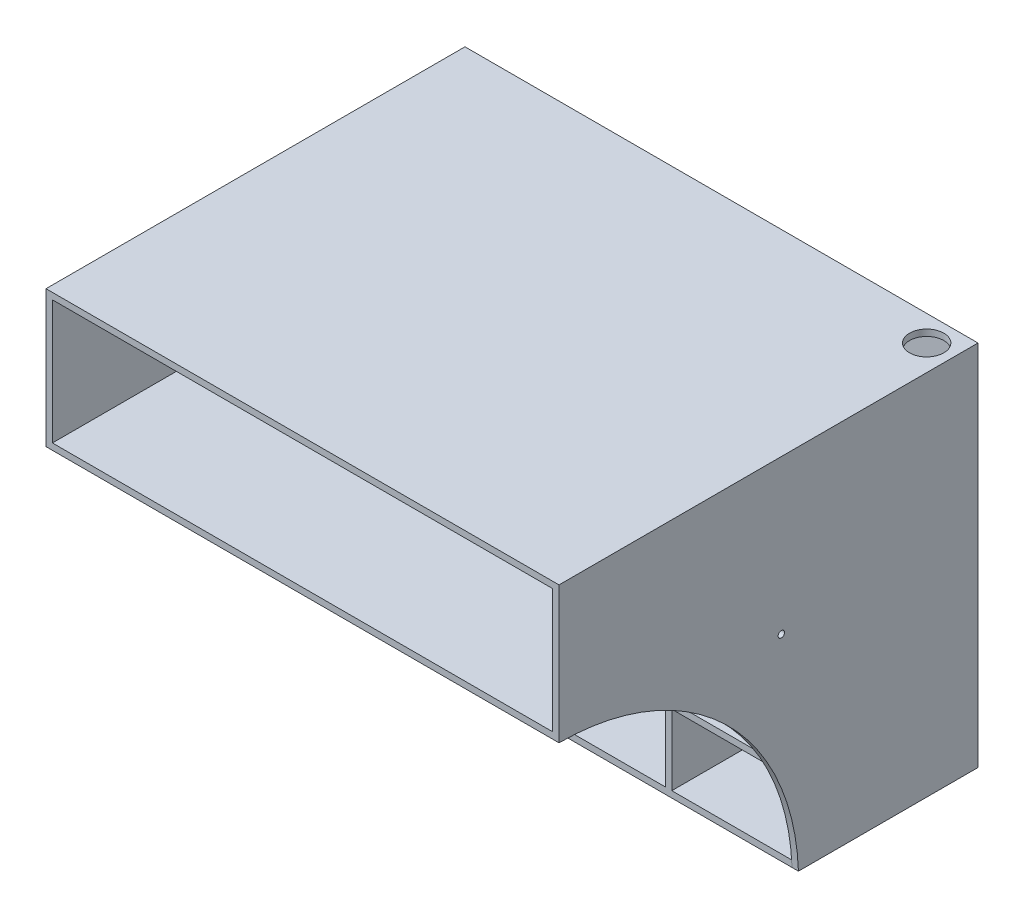
SolidWorks part; units mm, degrees
ref_plane "Front Plane" through (0, 0, 0) normal (0, 0, 1) x (1, 0, 0)
ref_plane "Top Plane" through (0, 0, 0) normal (0, 1, 0) x (1, 0, 0)
ref_plane "Right Plane" through (0, 0, 0) normal (1, 0, 0) x (0, 0, -1)
sketch "Sketch4" plane through (0, 0, 0) normal (0, 0, 1) x (1, 0, 0)
  line L1 (-381, -273.05) -> (381, -273.05)
  line L2 (-381, -273.05) -> (-381, 273.05)
  line L3 (-381, 273.05) -> (381, 273.05)
  line L4 (381, -273.05) -> (381, 273.05)
  line L5 (-381, -273.05) -> (381, 273.05) construction
  line L6 (-381, 273.05) -> (381, -273.05) construction
  point P0 (0, 0)
  dimension "D1" = 762
  dimension "D2" = 546.1
extrude "Boss-Extrude4" add sketch "Sketch4" along normal mid plane 190.5
shell "Shell1" thickness 9.525
sketch "Sketch5" plane through (0, 0, 95.25) normal (0, 0, 1) x (1, 0, 0)
  line L0 (-381, 268.2875) -> (381, 268.2875) construction
  line L1 (-371.475, -39.6875) -> (371.475, -39.6875)
  line L2 (-381, 273.05) -> (-381, -273.05) construction
  line L3 (381, -273.05) -> (381, 273.05) construction
  line L4 (-371.475, -153.9875) -> (371.475, -153.9875)
  line L5 (-188.1188, 74.6125) -> (-188.1188, -268.2875)
  line L6 (-381, -268.2875) -> (381, -268.2875) construction
  line L7 (-381, -273.05) -> (-381, -263.525) construction
  line L8 (-381, -273.05) -> (381, -273.05) construction
  line L9 (-371.475, -263.525) -> (371.475, -263.525) construction
  line L10 (-381, 263.525) -> (-381, 273.05) construction
  line L11 (371.475, 263.525) -> (-371.475, 263.525) construction
  line L12 (-376.2375, -268.2875) -> (-376.2375, 268.2875) construction
  line L13 (376.2375, 268.2875) -> (376.2375, -268.2875) construction
  line L14 (381, 0) -> (371.475, 0) construction
  line L15 (371.475, -263.525) -> (371.475, 263.525) construction
  line L16 (-371.475, 0) -> (-381, 0) construction
  line L17 (-371.475, 263.525) -> (-371.475, -263.525) construction
  line L18 (0, 74.6125) -> (0, -268.2875)
  line L19 (188.1188, 74.6125) -> (188.1188, -268.2875)
  line L20 (-376.2375, 242.8875) -> (-188.1188, 242.8875) construction
  line L21 (-371.475, 74.6125) -> (371.475, 74.6125)
  line L22 (-371.475, 74.6125) -> (-371.475, -39.6875) construction
  line L23 (-188.1188, 242.8875) -> (0, 242.8875) construction
  line L24 (188.1188, 242.8875) -> (376.2375, 242.8875) construction
  line L25 (-188.1188, 74.6125) -> (0, 74.6125) construction
  line L26 (0, 242.8875) -> (188.1188, 242.8875) construction
  point P11 (-381, -268.2875)
  point P22 (-381, 268.2875)
  point P30 (376.2375, 0)
  point P34 (-376.2375, 0)
  dimension "D1" = 114.3
  dimension "D3" = 114.3
  dimension "D4" = 25.4
  dimension "D6" = 3
  dimension "D2" = 3
rib "Rib1" sketch "Sketch5" sketch "Sketch5" thickness 9.525 extrusion direction normal to sketch draft on no parameters "D1"=9.525
sketch "Sketch23" plane through (0, 0, 95.25) normal (0, 0, 1) x (1, 0, 0)
  line L1 (-371.475, 263.525) -> (371.475, 263.525)
  line L2 (-371.475, 263.525) -> (-371.475, 79.375)
  line L3 (-371.475, 79.375) -> (371.475, 79.375)
  line L4 (371.475, 263.525) -> (371.475, 79.375)
extrude "Cut-Extrude9" cut sketch "Sketch23" against normal up to surface (180.975 mm away) up to face at (-282.1781, 171.45, -85.725)
sketch "Sketch8" plane through (0, 0, -95.25) normal (0, 0, -1) x (-1, 0, 0)
  line L4 (-381, -273.05) -> (381, -273.05)
  line L5 (381, -273.05) -> (381, 273.05)
  line L6 (381, 273.05) -> (-381, 273.05)
  line L7 (-381, 273.05) -> (-381, -273.05)
  line L8 (-381, -273.05) -> (381, -273.05)
  line L9 (381, -273.05) -> (381, 273.05)
  line L10 (381, 273.05) -> (-381, 273.05)
  line L11 (-381, 273.05) -> (-381, -273.05)
  dimension "D1" = 0
extrude "Boss-Extrude6" add sketch "Sketch8" along normal blind 76.2
sketch "Sketch9" plane through (0, 0, -171.45) normal (0, 0, -1) x (-1, 0, 0)
  line L0 (-381, 273.05) -> (-381, -273.05) construction
  line L3 (-371.475, -12.7) -> (371.475, -12.7)
  line L4 (-371.475, -12.7) -> (-371.475, -139.7)
  line L5 (-371.475, -139.7) -> (371.475, -139.7)
  line L6 (371.475, -12.7) -> (371.475, -139.7)
  line L8 (-371.475, -139.7) -> (371.475, -12.7) construction
  line L9 (-371.475, -12.7) -> (371.475, -139.7) construction
  point P10 (0, -76.2)
  dimension "D4" = 127
  dimension "D5" = 9.525
  dimension "D1" = 76.2
extrude "Access-Hole" cut sketch "Sketch9" against normal blind 9.525
sketch "Sketch19" plane through (0, 0, -161.925) normal (0, 0, -1) x (-1, 0, 0)
  line L0 (381, 273.05) -> (-381, 273.05) construction
  line L1 (-371.475, 263.525) -> (371.475, 263.525)
  line L2 (-371.475, 263.525) -> (-371.475, -263.525)
  line L3 (-371.475, -263.525) -> (371.475, -263.525)
  line L4 (371.475, 263.525) -> (371.475, -263.525)
  line L5 (-381, -273.05) -> (381, -273.05) construction
  line L6 (-371.475, -12.7) -> (-371.475, -139.7) construction
  line L7 (371.475, -139.7) -> (371.475, -12.7) construction
  dimension "D1" = 9.525
  dimension "D2" = 9.525
extrude "Space-Behind" cut sketch "Sketch19" against normal offset from surface (66.675 mm away) 9.525 up to face at (0, 171.45, -85.725)
sketch "Sketch12" plane through (0, 0, -85.725) normal (0, 0, 1) x (1, 0, 0)
  line L0 (-371.475, -158.75) -> (-192.8813, -158.75) construction
  line L2 (-244.0781, -158.75) -> (-320.2781, -158.75)
  arc A0 (-244.0781, -158.75) -> (-320.2781, -158.75) centre (-282.1781, -158.75) cw
  point P6 (-282.1781, -158.75)
  dimension "D1" = 38.1
extrude "Cable-Route" cut sketch "Sketch12" against normal up to surface (9.525 mm away) up to face at (0, 0, -95.25)
pattern_linear "Cable-Route-Pattern" count 4 spacing 187.325 along (1, 0, 0) count 3 spacing 114.3 along (0, 1, 0) of "Cable-Route"
sketch "Sketch16" plane through (-654.05, 273.05, 0) normal (0, -1, 0) x (0, 0, -1)
  line L0 (-95.25, 1035.05) -> (171.45, 1035.05) construction
  line L1 (171.45, 273.05) -> (171.45, 1035.05) construction
  circle A0 centre (133.35, 996.95) radius 25.4
  dimension "D3" = 50.8
  dimension "D2" = 38.1
  dimension "D1" = 38.1
extrude "Plug-Route" cut sketch "Sketch16" along normal up to next
sketch "Sketch24" plane through (0, 0, 95.25) normal (0, 0, 1) x (1, 0, 0)
  line L0 (130.5719, 69.85) -> (183.3563, 69.85) construction
  line L1 (-381, 273.05) -> (381, 273.05)
  line L2 (-381, 273.05) -> (-381, 69.85)
  line L3 (-381, 69.85) -> (381, 69.85)
  line L4 (381, 273.05) -> (381, 69.85)
  line L5 (381, -273.05) -> (381, 273.05) construction
  line L7 (-371.475, 263.525) -> (371.475, 263.525)
  line L8 (-371.475, 263.525) -> (-371.475, 79.375)
  line L9 (-371.475, 79.375) -> (371.475, 79.375)
  line L10 (371.475, 263.525) -> (371.475, 79.375)
extrude "Boss-Extrude7" add sketch "Sketch24" along normal blind 355.6
sketch "Sketch25" plane through (-381, 0, 0) normal (-1, 0, 0) x (0, 0, 1)
  line L0 (450.85, 69.85) -> (95.25, 69.85) construction
  line L3 (95.25, -273.05) -> (95.25, 69.85)
  line L4 (95.25, 69.85) -> (450.85, 69.85)
  arc A0 (95.25, -273.05) -> (450.85, 69.85) centre (450.85, -285.9852) cw
extrude "Boss-Extrude8" add sketch "Sketch25" against normal blind 9.525
mirror "Mirror1" about plane through (0, 0, 0) normal (1, 0, 0) of "Boss-Extrude8"
sketch "Sketch26" plane through (0, 0, 95.25) normal (0, 0, 1) x (1, 0, 0)
  line L0 (-183.3563, -34.925) -> (-4.7625, -34.925) construction
  line L1 (-183.3563, -44.45) -> (-4.7625, -44.45) construction
  line L2 (-192.8813, 69.85) -> (-192.8813, -34.925) construction
  line L5 (-4.7625, -44.45) -> (-4.7625, -149.225) construction
  line L10 (4.7625, -34.925) -> (183.3563, -34.925) construction
  line L12 (-192.8813, -44.45) -> (-192.8813, -149.225) construction
  line L14 (-183.3563, -149.225) -> (-4.7625, -149.225) construction
  line L15 (4.7625, -44.45) -> (4.7625, -149.225) construction
  line L16 (192.8813, -44.45) -> (192.8813, -149.225) construction
  line L17 (4.7625, -158.75) -> (183.3563, -158.75) construction
  line L18 (192.8813, -34.925) -> (371.475, -34.925) construction
  line L19 (183.3563, 69.85) -> (183.3563, -34.925) construction
  circle A0 centre (-188.1188, -39.6875) radius 4.7625
  circle A6 centre (0, -39.6875) radius 4.7625
  circle A7 centre (188.1188, -39.6875) radius 4.7625
  circle A8 centre (188.1188, -153.9875) radius 4.7625
  circle A9 centre (0, -153.9875) radius 4.7625
  circle A10 centre (-188.1188, -153.9875) radius 4.7625
extrude "Cut-Extrude10" cut sketch "Sketch26" against normal up to next
sketch "Sketch27" plane through (-381, 0, 0) normal (-1, 0, 0) x (0, 0, 1)
  line L0 (95.25, -34.925) -> (95.25, -44.45) construction
  line L1 (450.85, 69.85) -> (-85.725, 69.85) construction
  circle A0 centre (120.65, 44.45) radius 4.7625
  dimension "D1" = 9.525
  dimension "D2" = 25.4
  dimension "D3" = 25.4
extrude "Cut-Extrude11" cut sketch "Sketch27" against normal through all
equation "\"W\"= 3 / 8"
equation "\"D1@Shell1\"=\"W\""
equation "\"D1@Rib1\"=\"W\""
equation "\"D5@Sketch9\"=\"W\""
equation "\"D1@Access-Hole\" = \"W\""
equation "\"D2@Sketch19\"=\"W\""
equation "\"D1@Sketch19\"=\"W\""
equation "\"D1@Space-Behind\" = \"W\""
equation "\"D1@Boss-Extrude8\"=\"W\""
